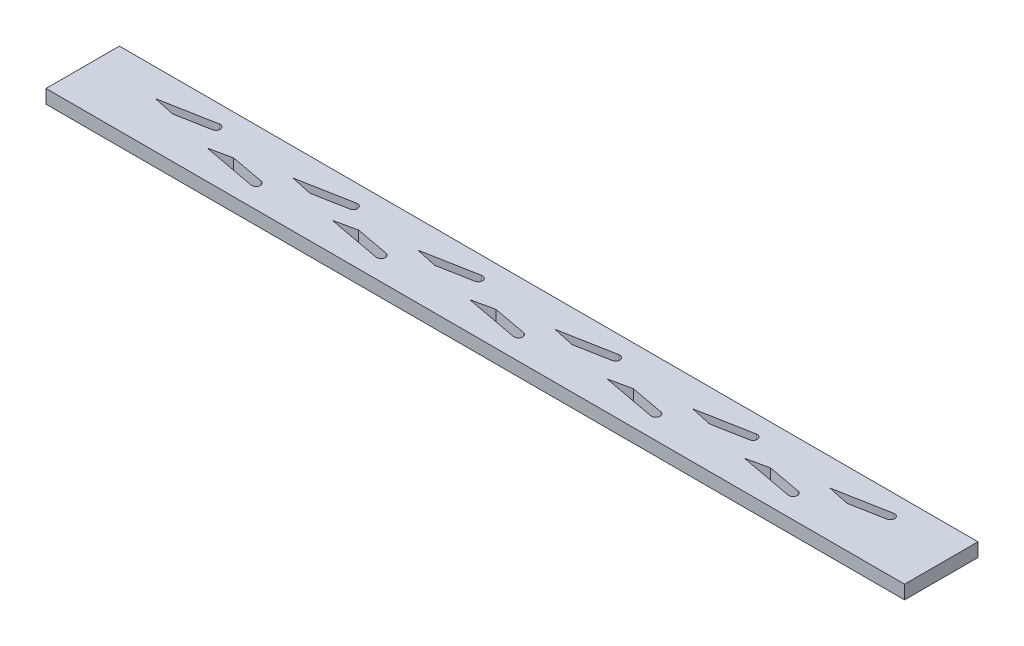
SolidWorks part; units mm, degrees
ref_plane "Front Plane" through (0, 0, 0) normal (0, 0, 1) x (1, 0, 0)
ref_plane "Top Plane" through (0, 0, 0) normal (0, 1, 0) x (1, 0, 0)
ref_plane "Right Plane" through (0, 0, 0) normal (1, 0, 0) x (0, 0, -1)
sketch "Sketch4" plane through (0, 0, 0) normal (0, 1, 0) x (1, 0, 0)
  line L1 (0, 0) -> (200, 0)
  line L2 (0, 0) -> (0, 17.1)
  line L3 (0, 17.1) -> (200, 17.1)
  line L4 (200, 0) -> (200, 17.1)
  dimension "D1" = 17.1
  dimension "D2" = 200
extrude "Boss-Extrude2" add sketch "Sketch4" along normal blind 3.175
sketch "Sketch5" plane through (0, 3.175, 0) normal (0, 1, 0) x (1, 0, 0)
  line L0 (0, 0) -> (200, 0) construction
  line L1 (-2.8998, -10.2189) -> (-2.8998, -27.2189) construction
  line L2 (0, 0) -> (200, 0)
  line L3 (0, 0) -> (0, 17.1)
  line L4 (0, 17.1) -> (200, 17.1)
  line L5 (200, 0) -> (200, 17.1)
  line L6 (11.5393, 2.25) -> (11.5393, 15.2) construction
  line L7 (72.6396, 14.9684) -> (72.6396, 2.0184) construction
  line L8 (88.6396, 14.9684) -> (88.6396, 2.0184) construction
  line L9 (30.8216, 6.75) -> (35.8574, 7.847)
  line L10 (35.8574, 7.847) -> (43.7223, 6.3831)
  line L11 (30.8216, 6.75) -> (43.3564, 4.4169)
  line L12 (46.8216, 10.7) -> (51.8574, 9.603)
  line L13 (46.8216, 10.7) -> (59.3564, 13.0331)
  line L14 (51.8574, 9.603) -> (59.7223, 11.0669)
  line L15 (104.6396, 14.9684) -> (104.6396, 2.0184) construction
  line L16 (120.6396, 14.9684) -> (120.6396, 2.0184) construction
  line L17 (136.6396, 14.9684) -> (136.6396, 2.0184) construction
  line L18 (152.6396, 14.9684) -> (152.6396, 2.0184) construction
  line L19 (168.6396, 14.9684) -> (168.6396, 2.0184) construction
  line L20 (184.6396, 14.9684) -> (184.6396, 2.0184) construction
  line L21 (14.8216, 10.7) -> (19.8574, 9.603)
  line L22 (19.8574, 9.603) -> (27.7223, 11.0669)
  line L23 (14.8216, 10.7) -> (27.3564, 13.0331)
  line L24 (75.9218, 10.7) -> (80.9576, 9.603)
  line L25 (80.9576, 9.603) -> (88.8225, 11.0669)
  line L26 (75.9218, 10.7) -> (88.4566, 13.0331)
  line L27 (107.9218, 10.7) -> (112.9576, 9.603)
  line L28 (112.9576, 9.603) -> (120.8225, 11.0669)
  line L29 (107.9218, 10.7) -> (120.4566, 13.0331)
  line L30 (139.9218, 10.7) -> (144.9576, 9.603)
  line L31 (144.9576, 9.603) -> (152.8225, 11.0669)
  line L32 (139.9218, 10.7) -> (152.4566, 13.0331)
  line L33 (171.9218, 10.7) -> (176.9576, 9.603)
  line L34 (176.9576, 9.603) -> (184.8225, 11.0669)
  line L35 (171.9218, 10.7) -> (184.4566, 13.0331)
  line L36 (59.9218, 6.75) -> (72.4566, 4.4169)
  line L37 (64.9576, 7.847) -> (72.8225, 6.3831)
  line L38 (59.9218, 6.75) -> (64.9576, 7.847)
  line L39 (91.9218, 6.75) -> (104.4566, 4.4169)
  line L40 (96.9576, 7.847) -> (104.8225, 6.3831)
  line L41 (91.9218, 6.75) -> (96.9576, 7.847)
  line L42 (59.5393, 15.2) -> (59.5393, 2.25) construction
  line L43 (0, 8.55) -> (200, 8.55) construction
  line L44 (0, 2.25) -> (200, 2.25) construction
  line L45 (200, 15.2) -> (0, 15.2) construction
  line L46 (43.5393, 2.25) -> (43.5393, 15.2) construction
  line L47 (0, 5.4) -> (200, 5.4) construction
  line L48 (0, 12.05) -> (200, 12.05) construction
  line L49 (27.5393, 15.2) -> (27.5393, 2.25) construction
  line L50 (123.9218, 6.75) -> (136.4566, 4.4169)
  line L51 (128.9576, 7.847) -> (136.8225, 6.3831)
  line L52 (123.9218, 6.75) -> (128.9576, 7.847)
  line L53 (155.9218, 6.75) -> (168.4566, 4.4169)
  line L54 (160.9576, 7.847) -> (168.8225, 6.3831)
  line L55 (155.9218, 6.75) -> (160.9576, 7.847)
  circle A0 centre (88.6396, 12.05) radius 3.15 construction
  arc A1 (43.7223, 6.3831) -> (43.3564, 4.4169) centre (43.5393, 5.4) cw
  arc A2 (59.3564, 13.0331) -> (59.7223, 11.0669) centre (59.5393, 12.05) cw
  circle A3 centre (120.6396, 12.05) radius 3.15 construction
  circle A4 centre (152.6396, 12.05) radius 3.15 construction
  circle A5 centre (184.6396, 12.05) radius 3.15 construction
  circle A6 centre (72.6396, 5.4) radius 3.15 construction
  circle A7 centre (104.6396, 5.4) radius 3.15 construction
  circle A8 centre (136.6396, 5.4) radius 3.15 construction
  circle A9 centre (168.6396, 5.4) radius 3.15 construction
  circle A10 centre (27.5393, 12.05) radius 3.15 construction
  arc A11 (27.3564, 13.0331) -> (27.7223, 11.0669) centre (27.5393, 12.05) cw
  arc A12 (88.4566, 13.0331) -> (88.8225, 11.0669) centre (88.6396, 12.05) cw
  arc A13 (120.4566, 13.0331) -> (120.8225, 11.0669) centre (120.6396, 12.05) cw
  arc A14 (152.4566, 13.0331) -> (152.8225, 11.0669) centre (152.6396, 12.05) cw
  circle A15 centre (43.5393, 5.4) radius 3.15 construction
  circle A16 centre (59.5393, 12.05) radius 3.15 construction
  arc A17 (184.4566, 13.0331) -> (184.8225, 11.0669) centre (184.6396, 12.05) cw
  arc A18 (72.8225, 6.3831) -> (72.4566, 4.4169) centre (72.6396, 5.4) cw
  arc A19 (104.8225, 6.3831) -> (104.4566, 4.4169) centre (104.6396, 5.4) cw
  arc A20 (136.8225, 6.3831) -> (136.4566, 4.4169) centre (136.6396, 5.4) cw
  arc A21 (168.8225, 6.3831) -> (168.4566, 4.4169) centre (168.6396, 5.4) cw
  dimension "D22" = 6.3
  dimension "D1" = 200
  dimension "D2" = 200
  dimension "D3" = 17
  dimension "D4" = 5.1539
  dimension "D5" = 2.25
  dimension "D6" = 3.15
  dimension "D7" = 16
  dimension "D8" = 16
  dimension "D9" = 3.15
  dimension "D10" = 3.5
  dimension "D11" = 4.5
  dimension "D12" = 4.5
  dimension "D13" = 27.5393
  dimension "D14" = 5.1539
  dimension "D15" = 12.75
  dimension "D16" = 8
  dimension "D17" = 2
  dimension "D18" = 2
  dimension "D19" = 8
  dimension "D20" = 12.75
  dimension "D21" = 3.15
  dimension "D23" = 16
extrude "Cut-Extrude3" cut sketch "Sketch5" against normal blind 3.175 contours A2 L13 L12 L14 | A18 L37 L38 L36 | A12 L26 L24 L25 | A19 L40 L41 L39 | A13 L29 L27 L28 | A14 L32 L30 L31 | A17 L35 L33 L34 | L21 L22 A11 L23 | L10 A1 L11 L9 | L51 A20 L50 L52 | L53 A21 L54 L55
sketch "Sketch2" plane through (0, 0, 0) normal (0, 1, 0) x (1, 0, 0)
  line L0 (240.7868, 258.8081) -> (423.9116, 240.5299) construction
  line L1 (0, 0) -> (200, 0) construction
  line L2 (0, -9.9873) -> (0, -26.9873) construction
  line L3 (0, 0) -> (200, 0)
  line L4 (0, 0) -> (0, 17.1)
  line L5 (0, 17.1) -> (200, 17.1)
  line L6 (200, 0) -> (200, 17.1)
  line L7 (11.5393, 2.25) -> (11.5393, 15.2) construction
  line L8 (75.5393, 15.2) -> (75.5393, 2.25) construction
  line L9 (91.5393, 15.2) -> (91.5393, 2.25) construction
  line L10 (30.8216, 6.75) -> (35.8574, 7.847)
  line L11 (35.8574, 7.847) -> (43.7223, 6.3831)
  line L12 (30.8216, 6.75) -> (43.3564, 4.4169)
  line L13 (46.8216, 10.7) -> (51.8574, 9.603)
  line L14 (46.8216, 10.7) -> (59.3564, 13.0331)
  line L15 (51.8574, 9.603) -> (59.7223, 11.0669)
  line L16 (107.5393, 15.2) -> (107.5393, 2.25) construction
  line L17 (123.5393, 15.2) -> (123.5393, 2.25) construction
  line L18 (139.5393, 15.2) -> (139.5393, 2.25) construction
  line L19 (155.5393, 15.2) -> (155.5393, 2.25) construction
  line L20 (171.5393, 15.2) -> (171.5393, 2.25) construction
  line L21 (187.5393, 15.2) -> (187.5393, 2.25) construction
  line L22 (14.8216, 10.7) -> (19.8574, 9.603)
  line L23 (19.8574, 9.603) -> (27.7223, 11.0669)
  line L24 (14.8216, 10.7) -> (27.3564, 13.0331)
  line L25 (78.8216, 10.7) -> (83.8574, 9.603)
  line L26 (83.8574, 9.603) -> (91.7223, 11.0669)
  line L27 (78.8216, 10.7) -> (91.3564, 13.0331)
  line L28 (110.8216, 10.7) -> (115.8574, 9.603)
  line L29 (115.8574, 9.603) -> (123.7223, 11.0669)
  line L30 (110.8216, 10.7) -> (123.3564, 13.0331)
  line L31 (142.8216, 10.7) -> (147.8574, 9.603)
  line L32 (147.8574, 9.603) -> (155.7223, 11.0669)
  line L33 (142.8216, 10.7) -> (155.3564, 13.0331)
  line L34 (174.8216, 10.7) -> (179.8574, 9.603)
  line L35 (179.8574, 9.603) -> (187.7223, 11.0669)
  line L36 (174.8216, 10.7) -> (187.3564, 13.0331)
  line L37 (62.8216, 6.75) -> (75.3564, 4.4169)
  line L38 (67.8574, 7.847) -> (75.7223, 6.3831)
  line L39 (62.8216, 6.75) -> (67.8574, 7.847)
  line L40 (94.8216, 6.75) -> (107.3564, 4.4169)
  line L41 (99.8574, 7.847) -> (107.7223, 6.3831)
  line L42 (94.8216, 6.75) -> (99.8574, 7.847)
  line L43 (59.5393, 15.2) -> (59.5393, 2.25) construction
  line L44 (0, 8.55) -> (200, 8.55) construction
  line L45 (0, 2.25) -> (200, 2.25) construction
  line L46 (200, 15.2) -> (0, 15.2) construction
  line L47 (43.5393, 2.25) -> (43.5393, 15.2) construction
  line L48 (0, 5.4) -> (200, 5.4) construction
  line L49 (0, 12.05) -> (200, 12.05) construction
  line L50 (27.5393, 15.2) -> (27.5393, 2.25) construction
  line L51 (126.8216, 6.75) -> (139.3564, 4.4169)
  line L52 (131.8574, 7.847) -> (139.7223, 6.3831)
  line L53 (126.8216, 6.75) -> (131.8574, 7.847)
  line L54 (158.8216, 6.75) -> (171.3564, 4.4169)
  line L55 (163.8574, 7.847) -> (171.7223, 6.3831)
  line L56 (158.8216, 6.75) -> (163.8574, 7.847)
  circle A0 centre (91.5393, 12.05) radius 3.15 construction
  arc A1 (43.7223, 6.3831) -> (43.3564, 4.4169) centre (43.5393, 5.4) cw
  arc A2 (59.3564, 13.0331) -> (59.7223, 11.0669) centre (59.5393, 12.05) cw
  circle A3 centre (123.5393, 12.05) radius 3.15 construction
  circle A4 centre (155.5393, 12.05) radius 3.15 construction
  circle A5 centre (187.5393, 12.05) radius 3.15 construction
  circle A6 centre (75.5393, 5.4) radius 3.15 construction
  circle A7 centre (107.5393, 5.4) radius 3.15 construction
  circle A8 centre (139.5393, 5.4) radius 3.15 construction
  circle A9 centre (171.5393, 5.4) radius 3.15 construction
  circle A10 centre (27.5393, 12.05) radius 3.15 construction
  arc A11 (27.3564, 13.0331) -> (27.7223, 11.0669) centre (27.5393, 12.05) cw
  arc A12 (91.3564, 13.0331) -> (91.7223, 11.0669) centre (91.5393, 12.05) cw
  arc A13 (123.3564, 13.0331) -> (123.7223, 11.0669) centre (123.5393, 12.05) cw
  arc A14 (155.3564, 13.0331) -> (155.7223, 11.0669) centre (155.5393, 12.05) cw
  circle A15 centre (43.5393, 5.4) radius 3.15 construction
  circle A16 centre (59.5393, 12.05) radius 3.15 construction
  arc A17 (187.3564, 13.0331) -> (187.7223, 11.0669) centre (187.5393, 12.05) cw
  arc A18 (75.7223, 6.3831) -> (75.3564, 4.4169) centre (75.5393, 5.4) cw
  arc A19 (107.7223, 6.3831) -> (107.3564, 4.4169) centre (107.5393, 5.4) cw
  arc A20 (139.7223, 6.3831) -> (139.3564, 4.4169) centre (139.5393, 5.4) cw
  arc A21 (171.7223, 6.3831) -> (171.3564, 4.4169) centre (171.5393, 5.4) cw
  dimension "D9" = 12.75
  dimension "D11" = 5.1539
  dimension "D12" = 12.75
  dimension "D13" = 3.15
  dimension "D14" = 8
  dimension "D15" = 2
  dimension "D16" = 2
  dimension "D18" = 3.15
  dimension "D21" = 16
  dimension "D25" = 5
  dimension "D19" = 6.3
  dimension "D1" = 200
  dimension "D2" = 200
  dimension "D3" = 3.5
  dimension "D4" = 17
  dimension "D5" = 4.5
  dimension "D6" = 8
  dimension "D7" = 4.5
  dimension "D8" = 27.5393
  dimension "D10" = 5.1539
  dimension "D17" = 2.25
  dimension "D20" = 3.15
  dimension "D22" = 16
  dimension "D23" = 16
  dimension "D24" = 9
  dimension "D26" = 5
  dimension "D27" = 2
  dimension "D28" = 2
  dimension "D29" = 5
  dimension "D30" = 5
